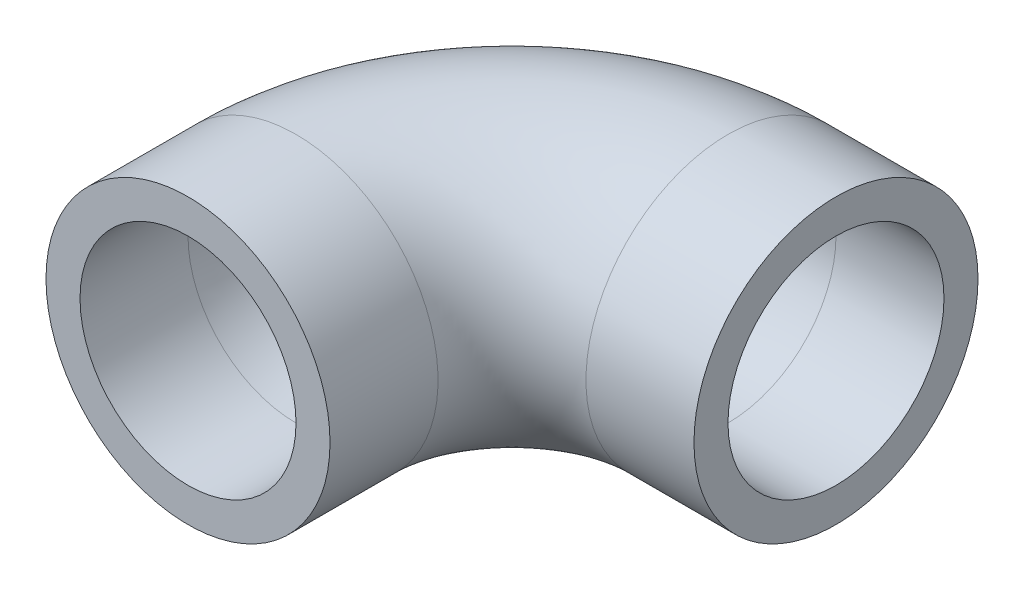
SolidWorks part; units mm, degrees
material "PVC Rigid"
ref_plane "Front Plane" through (0, 0, 0) normal (0, 0, 1) x (1, 0, 0)
ref_plane "Top Plane" through (0, 0, 0) normal (0, 1, 0) x (1, 0, 0)
ref_plane "Right Plane" through (0, 0, 0) normal (1, 0, 0) x (0, 0, -1)
sketch "Sketch1" plane through (0, 0, 0) normal (0, 0, 1) x (1, 0, 0)
  circle A0 centre (0, 0) radius 12.7
  circle A1 centre (0, 0) radius 16.7005
  dimension "D1" = 25.4
  dimension "D2" = 33.401
sketch "Sketch2" plane through (0, 0, 0) normal (0, 1, 0) x (1, 0, 0)
  line L0 (0, 0) -> (0, 12.7)
  line L1 (25.4, 38.1) -> (38.1, 38.1)
  arc A0 (0, 12.7) -> (25.4, 38.1) centre (25.4, 12.7) cw
  dimension "D1" = 25.4
  dimension "D2" = 12.7
sweep "Sweep1" add profiles "Sketch1" path "Sketch2"
